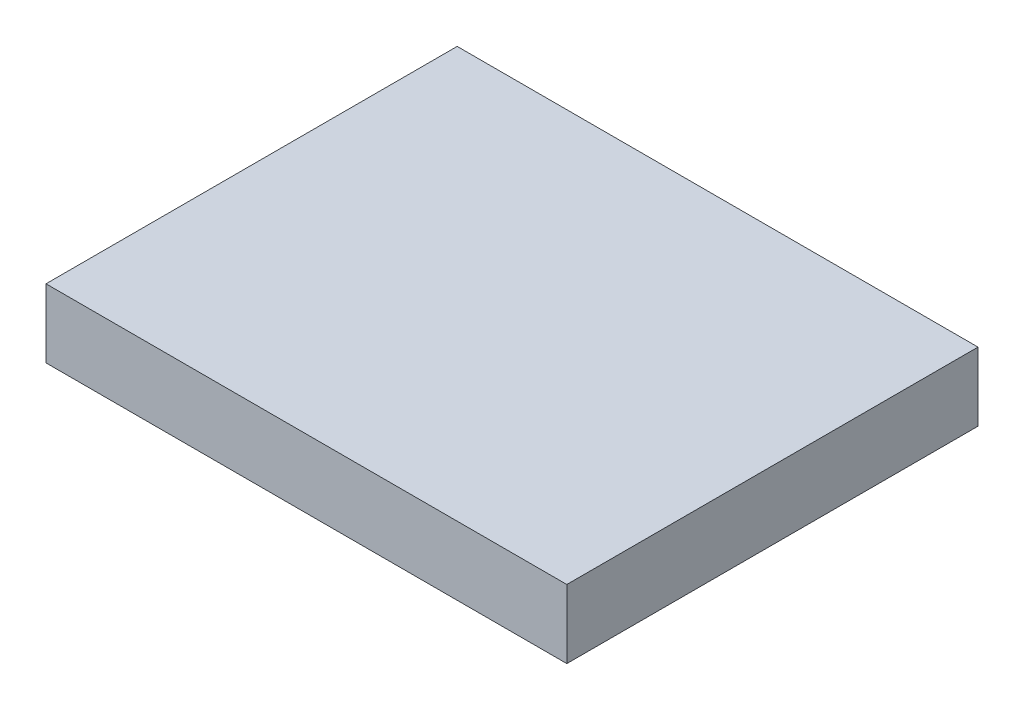
SolidWorks part; units mm, degrees
material "Custom Plastic"
ref_plane "Front Plane" through (0, 0, 0) normal (0, 0, 1) x (1, 0, 0)
ref_plane "Top Plane" through (0, 0, 0) normal (0, 1, 0) x (1, 0, 0)
ref_plane "Right Plane" through (0, 0, 0) normal (1, 0, 0) x (0, 0, -1)
sketch "Sketch1" plane through (0, 0, 0) normal (0, 1, 0) x (1, 0, 0)
  line L1 (9.652, -7.62) -> (-9.652, -7.62)
  line L2 (9.652, -7.62) -> (9.652, 7.62)
  line L3 (9.652, 7.62) -> (-9.652, 7.62)
  line L4 (-9.652, -7.62) -> (-9.652, 7.62)
  line L5 (9.652, -7.62) -> (-9.652, 7.62) construction
  line L6 (9.652, 7.62) -> (-9.652, -7.62) construction
  point P0 (0, 0)
extrude "Extrude1" add sketch "Sketch1" along normal blind 2.54
